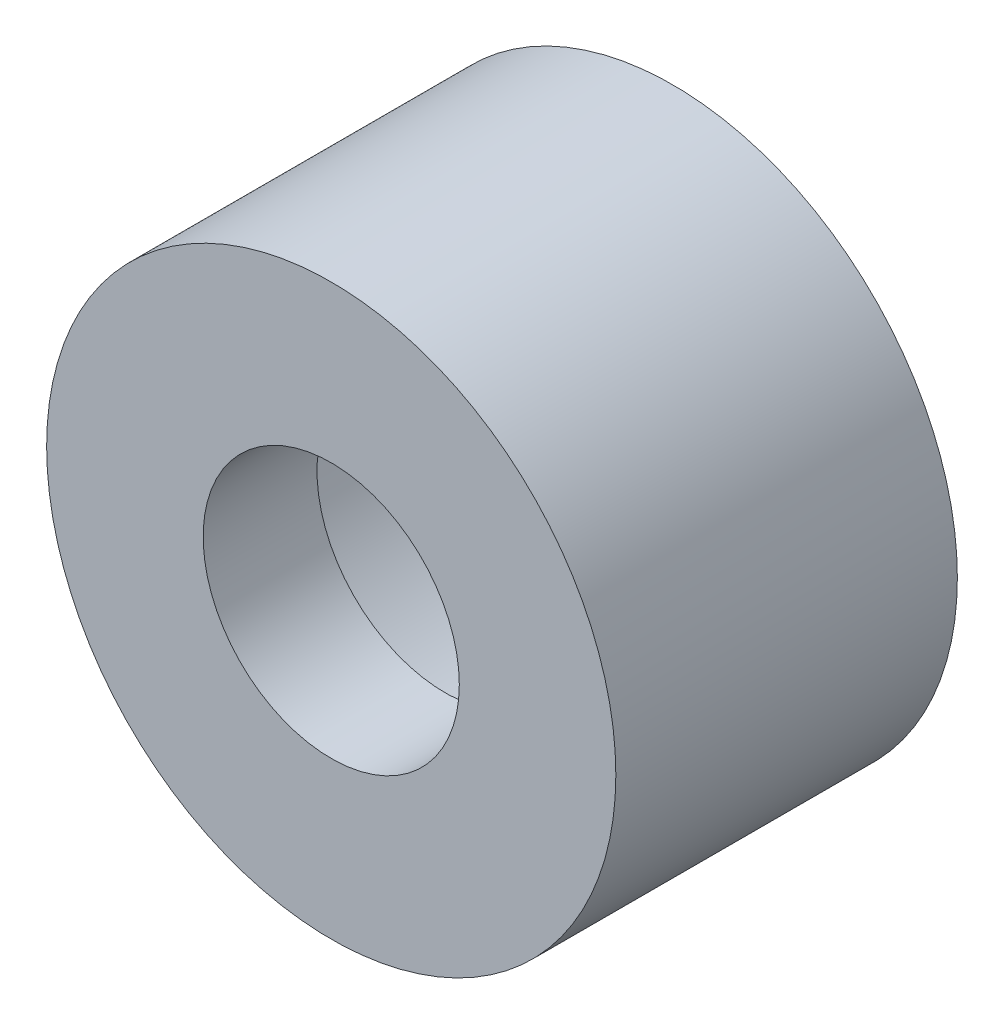
SolidWorks part; units mm, degrees
ref_plane "Alzado" through (0, 0, 0) normal (0, 0, 1) x (1, 0, 0)
ref_plane "Planta" through (0, 0, 0) normal (0, 1, 0) x (1, 0, 0)
ref_plane "Vista lateral" through (0, 0, 0) normal (1, 0, 0) x (0, 0, -1)
sketch "Croquis1" plane through (0, 0, 0) normal (0, 0, 1) x (1, 0, 0)
  circle A0 centre (0, 0) radius 5
  circle A1 centre (0, 0) radius 4.25
  dimension "D1" = 8.5
  dimension "D2" = 10
extrude "Saliente-Extruir1" add sketch "Croquis1" along normal blind 4
sketch "Croquis2" plane through (0, 0, 4) normal (0, 0, 1) x (1, 0, 0)
  circle A0 centre (0, 0) radius 5
  circle A1 centre (0, 0) radius 2.25
  dimension "D1" = 4.5
  dimension "D2" = 10
extrude "Saliente-Extruir2" add sketch "Croquis2" along normal blind 2
